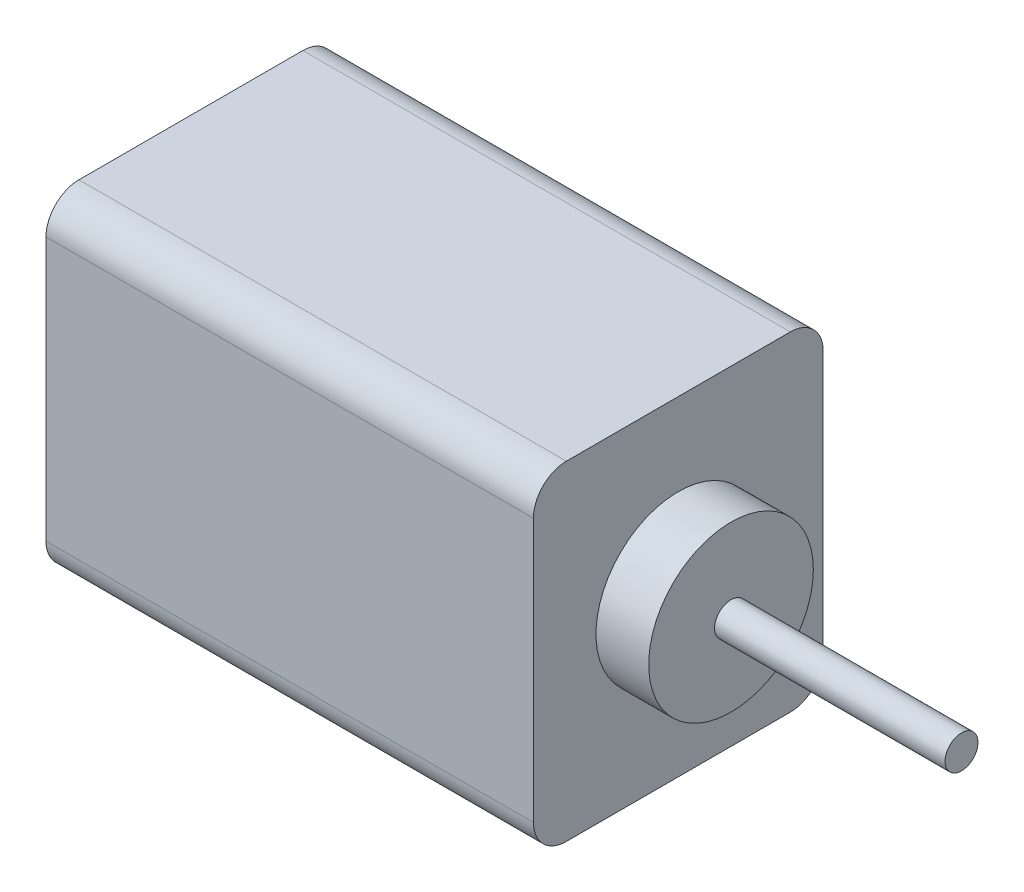
SolidWorks part; units mm, degrees
ref_plane "Front Plane" through (0, 0, 0) normal (0, 0, 1) x (1, 0, 0)
ref_plane "Top Plane" through (0, 0, 0) normal (0, 1, 0) x (1, 0, 0)
ref_plane "Right Plane" through (0, 0, 0) normal (1, 0, 0) x (0, 0, -1)
sketch "Sketch1" plane through (0, 0, 0) normal (0, 1, 0) x (1, 0, 0)
  line L1 (-37, 22) -> (37, 22)
  line L2 (-37, 22) -> (-37, -22)
  line L3 (-37, -22) -> (37, -22)
  line L4 (37, 22) -> (37, -22)
  line L5 (-37, 22) -> (37, -22) construction
  line L6 (-37, -22) -> (37, 22) construction
  point P0 (0, 0)
  dimension "D1" = 74
  dimension "D2" = 44
extrude "Boss-Extrude1" add sketch "Sketch1" along normal blind 50
sketch "Sketch2" plane through (37, 0, 0) normal (1, 0, 0) x (0, 0, -1)
  line L0 (0, 0) -> (0, 50) construction
  line L1 (-22, 50) -> (22, 50) construction
  circle A0 centre (0, 25) radius 12.5
  dimension "D1" = 25
extrude "Boss-Extrude2" add sketch "Sketch2" along normal blind 8
sketch "Sketch3" plane through (45, 0, 0) normal (1, 0, 0) x (0, 0, -1)
  line L0 (0, 37.5) -> (0, 12.5) construction
  circle A0 centre (0, 24.784) radius 2.5
  circle A1 centre (0, 25) radius 12.5 construction
  circle A2 centre (0, 25) radius 12.5 construction
extrude "Boss-Extrude3" add sketch "Sketch3" along normal blind 35
fillet "Fillet1" radius 5 4 edges at (0, 0, 22) (0, 0, -22) (0, 50, -22) (0, 50, 22)
